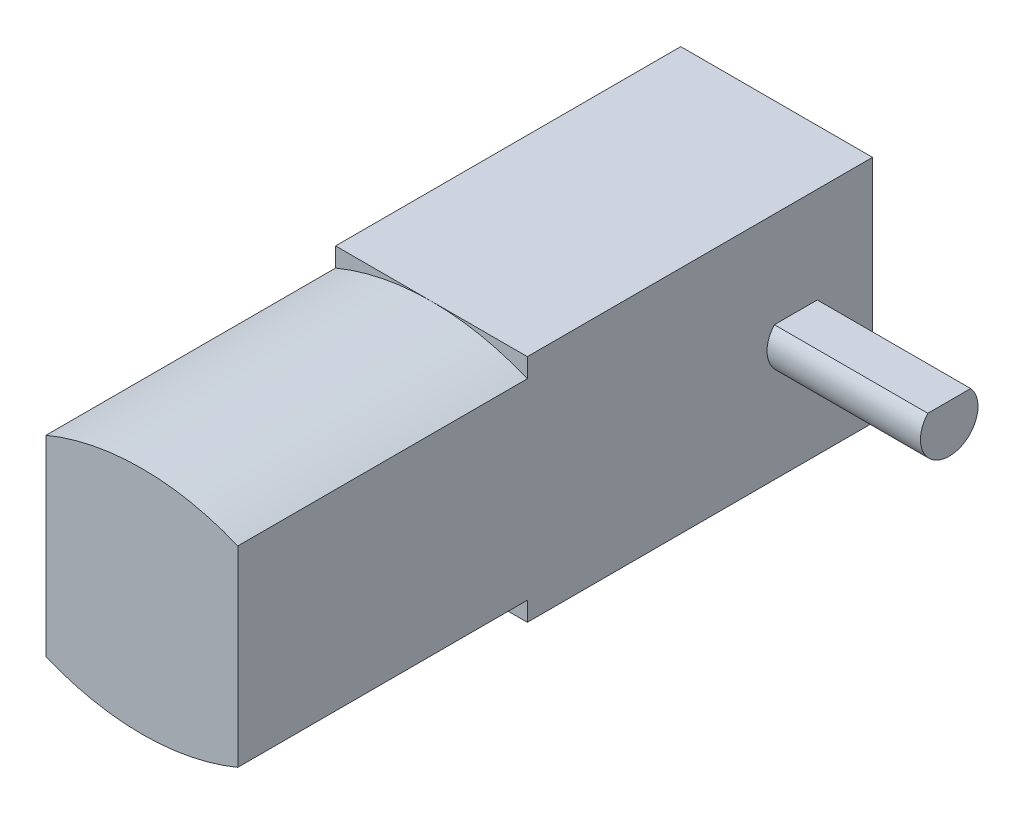
SolidWorks part; units mm, degrees
ref_plane "Front Plane" through (0, 0, 0) normal (0, 0, 1) x (1, 0, 0)
ref_plane "Top Plane" through (0, 0, 0) normal (0, 1, 0) x (1, 0, 0)
ref_plane "Right Plane" through (0, 0, 0) normal (1, 0, 0) x (0, 0, -1)
sketch "Sketch1" plane through (0, 0, 0) normal (0, 0, 1) x (1, 0, 0)
  line L0 (0, -6) -> (0, 6)
  line L1 (-5, -5) -> (5, -5)
  line L2 (-5, -5) -> (-5, 5)
  line L3 (-5, 5) -> (5, 5)
  line L4 (5, -5) -> (5, 5)
  line L5 (-5, -5) -> (5, 5) construction
  line L6 (-5, 5) -> (5, -5) construction
  arc A0 (0, 6) -> (-5, 5) centre (0, -7) ccw
  arc A1 (0, 6) -> (5, 5) centre (0, -7) cw
  arc A2 (0, -6) -> (-5, -5) centre (0, 7) cw
  arc A3 (0, -6) -> (5, -5) centre (0, 7) ccw
  point P0 (0, 0)
  point P9 (0, 0)
  dimension "D1" = 10
  dimension "D2" = 10
  dimension "D3" = 12
extrude "Boss-Extrude1" add sketch "Sketch1" along normal blind 15.1 contours L3 L2 L1 L0 | L1 L4 L3 L0 | A1 L0 L3 | L0 A0 L3 | L0 A3 L1 | A2 L0 L1
sketch "Sketch2" plane through (0, 0, 0) normal (0, 0, 1) x (1, 0, 0)
  line L1 (5, -6) -> (-5, -6)
  line L2 (5, -6) -> (5, 6)
  line L3 (5, 6) -> (-5, 6)
  line L4 (-5, -6) -> (-5, 6)
  line L5 (5, -6) -> (-5, 6) construction
  line L6 (5, 6) -> (-5, -6) construction
  point P0 (0, 0)
  dimension "D1" = 12
  dimension "D2" = 10
extrude "Boss-Extrude2" add sketch "Sketch2" against normal blind 18
sketch "Sketch3" plane through (5, 0, 0) normal (1, 0, 0) x (0, 0, -1)
  line L0 (18, 0) -> (14, 0)
  line L1 (18, -6) -> (18, 6) construction
  line L2 (14, -1.5) -> (14, 1)
  line L3 (15.118, 1) -> (12.882, 1)
  circle A0 centre (14, 0) radius 1.5
  circle A1 centre (14, 0) radius 9.5
  point P11 (14, 1)
  dimension "D2" = 3
  dimension "D4" = 19
  dimension "D1" = 4
  dimension "D3" = 2.5
extrude "Boss-Extrude3" add sketch "Sketch3" along normal blind 8 contours L3 A0 L2 | L0 A0 L3 L2 | L2 A0 L0
